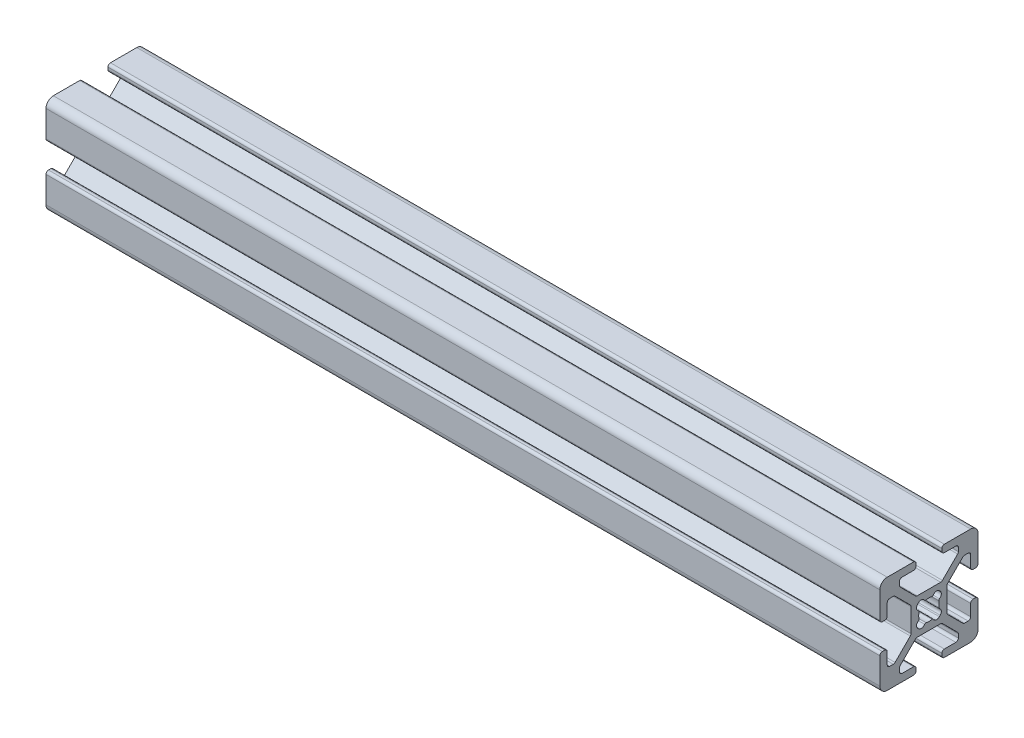
SolidWorks part; units mm, degrees
ref_plane "Front Plane" through (0, 0, 0) normal (0, 0, 1) x (1, 0, 0)
ref_plane "Top Plane" through (0, 0, 0) normal (0, 1, 0) x (1, 0, 0)
ref_plane "Right Plane" through (0, 0, 0) normal (1, 0, 0) x (0, 0, -1)
sketch "Sketch1" plane through (0, 0, 0) normal (0, 1, 0) x (1, 0, 0)
  line L0 (0, 0) -> (170, 0)
  dimension "D1" = 170
other "20_series 20-2020(1)"
ref_plane "Plane1" through (0, 0, 0) normal (1, 0, 0) x (0, 0, -1)
sketch "Sketch11" plane through (0, 0, 0) normal (1, 0, 0) x (0, 0, -1)
  line L0 (9.0094, 2.6289) -> (9.492, 2.6289)
  line L1 (8.5014, 5.4864) -> (8.5014, 3.1369)
  line L2 (10, 8.5014) -> (10, 3.1369)
  line L3 (7.2645, 5.9944) -> (7.9934, 5.9944)
  line L4 (3.1369, 10) -> (8.5014, 10)
  line L5 (3.8074, 2.7477) -> (6.9053, 5.8456)
  line L6 (2.6289, 9.0094) -> (2.6289, 9.492)
  line L7 (3.6586, -2.3885) -> (3.6586, 2.3885)
  line L8 (3.1369, 8.5014) -> (5.4864, 8.5014)
  line L9 (6.9053, -5.8456) -> (3.8074, -2.7477)
  line L10 (5.9944, 7.9934) -> (5.9944, 7.2645)
  line L11 (7.9934, -5.9944) -> (7.2645, -5.9944)
  line L12 (5.8456, 6.9053) -> (2.7477, 3.8074)
  line L13 (8.5014, -3.1369) -> (8.5014, -5.4864)
  line L14 (2.3885, 3.6586) -> (-2.3885, 3.6586)
  line L15 (9.0094, -2.6289) -> (9.492, -2.6289)
  line L16 (-2.7477, 3.8074) -> (-5.8456, 6.9053)
  line L17 (10, -3.1369) -> (10, -8.5014)
  line L18 (-5.9944, 7.2645) -> (-5.9944, 7.9934)
  line L19 (8.5014, -10) -> (3.1369, -10)
  line L20 (-5.4864, 8.5014) -> (-3.1369, 8.5014)
  line L21 (2.6289, -9.0094) -> (2.6289, -9.492)
  line L22 (-2.6289, 9.0094) -> (-2.6289, 9.492)
  line L23 (5.4864, -8.5014) -> (3.1369, -8.5014)
  line L24 (-8.5014, 10) -> (-3.1369, 10)
  line L25 (5.9944, -7.2645) -> (5.9944, -7.9934)
  line L26 (-10, 3.1369) -> (-10, 8.5014)
  line L27 (2.7477, -3.8074) -> (5.8456, -6.9053)
  line L28 (-9.0094, 2.6289) -> (-9.492, 2.6289)
  line L29 (-2.3885, -3.6586) -> (2.3885, -3.6586)
  line L30 (-8.5014, 3.1369) -> (-8.5014, 5.4864)
  line L31 (-5.8456, -6.9053) -> (-2.7477, -3.8074)
  line L32 (-7.9934, 5.9944) -> (-7.2645, 5.9944)
  line L33 (-5.9944, -7.9934) -> (-5.9944, -7.2645)
  line L34 (-6.9053, 5.8456) -> (-3.8074, 2.7477)
  line L35 (-3.1369, -8.5014) -> (-5.4864, -8.5014)
  line L36 (-3.6586, 2.3885) -> (-3.6586, -2.3885)
  line L37 (-2.6289, -9.0094) -> (-2.6289, -9.492)
  line L38 (-3.8074, -2.7477) -> (-6.9053, -5.8456)
  line L39 (-3.1369, -10) -> (-8.5014, -10)
  line L40 (-7.2645, -5.9944) -> (-7.9934, -5.9944)
  line L41 (-10, -8.5014) -> (-10, -3.1369)
  line L42 (-8.5014, -5.4864) -> (-8.5014, -3.1369)
  line L43 (-9.0094, -2.6289) -> (-9.492, -2.6289)
  line L44 (-2.2966, 2.1217) -> (-2.1217, 2.2966)
  line L45 (2.1217, 2.2966) -> (2.2966, 2.1217)
  line L46 (-2.1217, -2.2966) -> (-2.2966, -2.1217)
  line L47 (2.2966, -2.1217) -> (2.1217, -2.2966)
  arc A0 (8.5014, 3.1369) -> (9.0094, 2.6289) centre (9.0094, 3.1369) ccw
  arc A1 (9.492, 2.6289) -> (10, 3.1369) centre (9.492, 3.1369) ccw
  arc A2 (8.5014, 5.4864) -> (7.9934, 5.9944) centre (7.9934, 5.4864) ccw
  arc A3 (10, 8.5014) -> (8.5014, 10) centre (8.5014, 8.5014) ccw
  arc A4 (7.2645, 5.9944) -> (6.9053, 5.8456) centre (7.2645, 5.4864) ccw
  arc A5 (3.1369, 10) -> (2.6289, 9.492) centre (3.1369, 9.492) ccw
  arc A6 (3.8074, 2.7477) -> (3.6586, 2.3885) centre (4.1666, 2.3885) ccw
  arc A7 (2.6289, 9.0094) -> (3.1369, 8.5014) centre (3.1369, 9.0094) ccw
  arc A8 (3.6586, -2.3885) -> (3.8074, -2.7477) centre (4.1666, -2.3885) ccw
  arc A9 (5.9944, 7.9934) -> (5.4864, 8.5014) centre (5.4864, 7.9934) ccw
  arc A10 (6.9053, -5.8456) -> (7.2645, -5.9944) centre (7.2645, -5.4864) ccw
  arc A11 (5.8456, 6.9053) -> (5.9944, 7.2645) centre (5.4864, 7.2645) ccw
  arc A12 (7.9934, -5.9944) -> (8.5014, -5.4864) centre (7.9934, -5.4864) ccw
  arc A13 (2.3885, 3.6586) -> (2.7477, 3.8074) centre (2.3885, 4.1666) ccw
  arc A14 (9.0094, -2.6289) -> (8.5014, -3.1369) centre (9.0094, -3.1369) ccw
  arc A15 (-2.7477, 3.8074) -> (-2.3885, 3.6586) centre (-2.3885, 4.1666) ccw
  arc A16 (10, -3.1369) -> (9.492, -2.6289) centre (9.492, -3.1369) ccw
  arc A17 (-5.9944, 7.2645) -> (-5.8456, 6.9053) centre (-5.4864, 7.2645) ccw
  arc A18 (8.5014, -10) -> (10, -8.5014) centre (8.5014, -8.5014) ccw
  arc A19 (-5.4864, 8.5014) -> (-5.9944, 7.9934) centre (-5.4864, 7.9934) ccw
  arc A20 (2.6289, -9.492) -> (3.1369, -10) centre (3.1369, -9.492) ccw
  arc A21 (-3.1369, 8.5014) -> (-2.6289, 9.0094) centre (-3.1369, 9.0094) ccw
  arc A22 (3.1369, -8.5014) -> (2.6289, -9.0094) centre (3.1369, -9.0094) ccw
  arc A23 (-2.6289, 9.492) -> (-3.1369, 10) centre (-3.1369, 9.492) ccw
  arc A24 (5.4864, -8.5014) -> (5.9944, -7.9934) centre (5.4864, -7.9934) ccw
  arc A25 (-8.5014, 10) -> (-10, 8.5014) centre (-8.5014, 8.5014) ccw
  arc A26 (5.9944, -7.2645) -> (5.8456, -6.9053) centre (5.4864, -7.2645) ccw
  arc A27 (-10, 3.1369) -> (-9.492, 2.6289) centre (-9.492, 3.1369) ccw
  arc A28 (2.7477, -3.8074) -> (2.3885, -3.6586) centre (2.3885, -4.1666) ccw
  arc A29 (-9.0094, 2.6289) -> (-8.5014, 3.1369) centre (-9.0094, 3.1369) ccw
  arc A30 (-2.3885, -3.6586) -> (-2.7477, -3.8074) centre (-2.3885, -4.1666) ccw
  arc A31 (-7.9934, 5.9944) -> (-8.5014, 5.4864) centre (-7.9934, 5.4864) ccw
  arc A32 (-5.8456, -6.9053) -> (-5.9944, -7.2645) centre (-5.4864, -7.2645) ccw
  arc A33 (-6.9053, 5.8456) -> (-7.2645, 5.9944) centre (-7.2645, 5.4864) ccw
  arc A34 (-5.9944, -7.9934) -> (-5.4864, -8.5014) centre (-5.4864, -7.9934) ccw
  arc A35 (-3.6586, 2.3885) -> (-3.8074, 2.7477) centre (-4.1666, 2.3885) ccw
  arc A36 (-2.6289, -9.0094) -> (-3.1369, -8.5014) centre (-3.1369, -9.0094) ccw
  arc A37 (-3.8074, -2.7477) -> (-3.6586, -2.3885) centre (-4.1666, -2.3885) ccw
  arc A38 (-3.1369, -10) -> (-2.6289, -9.492) centre (-3.1369, -9.492) ccw
  arc A39 (-7.2645, -5.9944) -> (-6.9053, -5.8456) centre (-7.2645, -5.4864) ccw
  arc A40 (-10, -8.5014) -> (-8.5014, -10) centre (-8.5014, -8.5014) ccw
  arc A41 (-8.5014, -5.4864) -> (-7.9934, -5.9944) centre (-7.9934, -5.4864) ccw
  arc A42 (-9.492, -2.6289) -> (-10, -3.1369) centre (-9.492, -3.1369) ccw
  arc A43 (-8.5014, -3.1369) -> (-9.0094, -2.6289) centre (-9.0094, -3.1369) ccw
  arc A44 (-0.8806, 2.1293) -> (-0.5885, 2.0112) centre (-0.6599, 2.2549) ccw
  arc A45 (0.5885, 2.0112) -> (-0.5885, 2.0112) centre (0, 0) ccw
  arc A46 (-0.8806, 2.1293) -> (-2.1217, 2.2966) centre (-1.565, 1.7398) ccw
  arc A47 (0.5885, 2.0112) -> (0.8806, 2.1293) centre (0.6599, 2.2549) ccw
  arc A48 (2.1217, 2.2966) -> (0.8806, 2.1293) centre (1.565, 1.7398) ccw
  arc A49 (-2.2966, 2.1217) -> (-2.1293, 0.8806) centre (-1.7398, 1.565) ccw
  arc A50 (-2.0112, 0.5885) -> (-2.1293, 0.8806) centre (-2.2549, 0.6599) ccw
  arc A51 (2.1293, 0.8806) -> (2.2966, 2.1217) centre (1.7398, 1.565) ccw
  arc A52 (-2.0112, 0.5885) -> (-2.0112, -0.5885) centre (0, 0) ccw
  arc A53 (2.1293, 0.8806) -> (2.0112, 0.5885) centre (2.2549, 0.6599) ccw
  arc A54 (-2.1293, -0.8806) -> (-2.0112, -0.5885) centre (-2.2549, -0.6599) ccw
  arc A55 (2.0112, -0.5885) -> (2.0112, 0.5885) centre (0, 0) ccw
  arc A56 (-2.1293, -0.8806) -> (-2.2966, -2.1217) centre (-1.7398, -1.565) ccw
  arc A57 (2.0112, -0.5885) -> (2.1293, -0.8806) centre (2.2549, -0.6599) ccw
  arc A58 (2.2966, -2.1217) -> (2.1293, -0.8806) centre (1.7398, -1.565) ccw
  arc A59 (-2.1217, -2.2966) -> (-0.8806, -2.1293) centre (-1.565, -1.7398) ccw
  arc A60 (-0.5885, -2.0112) -> (-0.8806, -2.1293) centre (-0.6599, -2.2549) ccw
  arc A61 (0.8806, -2.1293) -> (2.1217, -2.2966) centre (1.565, -1.7398) ccw
  arc A62 (-0.5885, -2.0112) -> (0.5885, -2.0112) centre (0, 0) ccw
  arc A63 (0.8806, -2.1293) -> (0.5885, -2.0112) centre (0.6599, -2.2549) ccw
  point P0 (0, 0)
